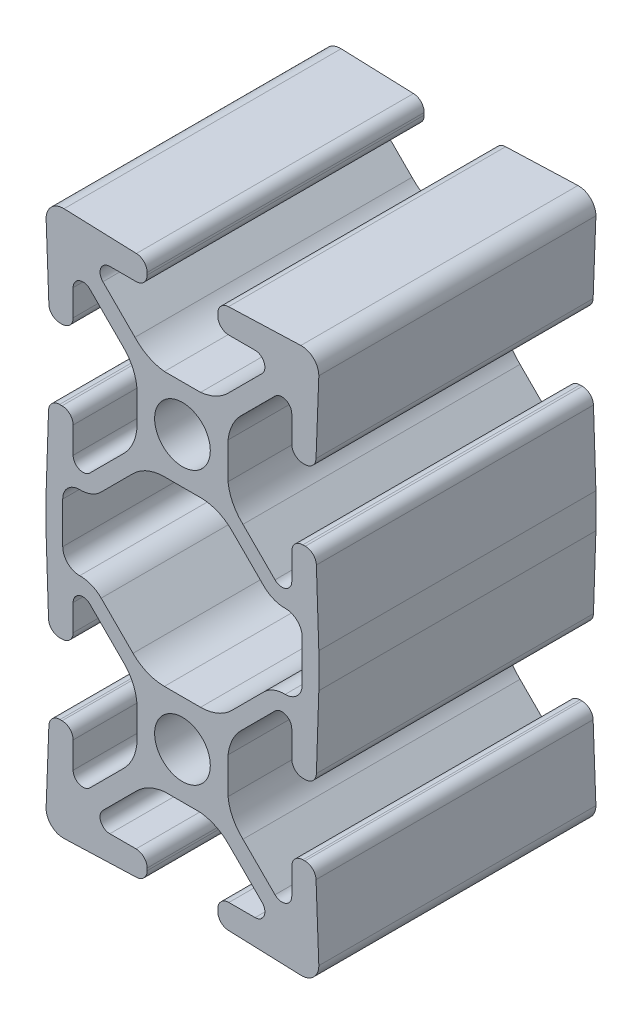
SolidWorks part; units mm, degrees
material "6061 Alloy"
ref_plane "Front" through (0, 0, 0) normal (0, 0, 1) x (1, 0, 0)
ref_plane "Top" through (0, 0, 0) normal (0, 1, 0) x (1, 0, 0)
ref_plane "Right" through (0, 0, 0) normal (1, 0, 0) x (0, 0, -1)
sketch "Sketch1" plane through (0, 0, 0) normal (0, 0, 1) x (1, 0, 0)
  line L0 (-4.5322, 5.3683) -> (-7.4494, 8.2856)
  line L1 (-10.976, 10.6094) -> (-10.976, 14.3906)
  line L2 (1.6585, 4.178) -> (-1.6585, 4.178)
  line L3 (7.4494, 8.2856) -> (4.5322, 5.3683)
  line L4 (-7.4494, 16.7144) -> (-4.5322, 19.6317)
  line L5 (-1.6585, 20.822) -> (1.6585, 20.822)
  line L6 (10.976, 14.3906) -> (10.976, 10.6094)
  line L7 (4.5322, 19.6317) -> (7.4494, 16.7144)
  line L8 (-8.4836, 7.2939) -> (-5.5451, 4.3554)
  line L9 (-10.02, 4.2545) -> (-10.02, 6.6575)
  line L10 (-4.178, 1.6585) -> (-4.178, -1.6585)
  line L11 (-11.2584, 3.2377) -> (-11.036, 3.2385)
  line L12 (-5.5451, -4.3554) -> (-8.4836, -7.2939)
  line L13 (-12.5, 10.9125) -> (-12.2773, 4.22)
  line L14 (-12.5, 14.0875) -> (-12.5, 10.9125)
  line L15 (-10.02, -6.6575) -> (-10.02, -4.2545)
  line L16 (-12.2773, 20.78) -> (-12.5, 14.0875)
  line L17 (-11.036, -3.2385) -> (-11.2263, -3.2379)
  line L18 (-11.036, 21.7615) -> (-11.2584, 21.7623)
  line L19 (-12.2451, -4.2152) -> (-12.5, -10.9135)
  line L20 (-10.02, 18.3425) -> (-10.02, 20.7455)
  line L21 (-10.8555, -12.5) -> (-4.2218, -12.2615)
  line L22 (-5.5451, 20.6446) -> (-8.4836, 17.7061)
  line L23 (-3.2385, -11.246) -> (-3.2385, -11.036)
  line L24 (-4.178, 26.6585) -> (-4.178, 23.3415)
  line L25 (-4.2545, -10.02) -> (-6.6575, -10.02)
  line L26 (-8.4836, 32.2939) -> (-5.5451, 29.3554)
  line L27 (-7.2939, -8.4836) -> (-4.3554, -5.5451)
  line L28 (-10.02, 29.2545) -> (-10.02, 31.6575)
  line L29 (-1.6585, -4.178) -> (1.6585, -4.178)
  line L30 (-11.2263, 28.2379) -> (-11.036, 28.2385)
  line L31 (4.3554, -5.5451) -> (7.2939, -8.4836)
  line L32 (-12.5, 35.9135) -> (-12.2451, 29.2152)
  line L33 (6.6575, -10.02) -> (4.2545, -10.02)
  line L34 (-4.2218, 37.2615) -> (-10.8555, 37.5)
  line L35 (3.2385, -11.036) -> (3.2385, -11.246)
  line L36 (-3.2385, 36.036) -> (-3.2385, 36.246)
  line L37 (4.2218, -12.2615) -> (10.8555, -12.5)
  line L38 (-6.6575, 35.02) -> (-4.2545, 35.02)
  line L39 (12.5, -10.9135) -> (12.2451, -4.2152)
  line L40 (-4.3554, 30.5451) -> (-7.2939, 33.4836)
  line L41 (11.2263, -3.2379) -> (11.036, -3.2385)
  line L42 (1.6585, 29.178) -> (-1.6585, 29.178)
  line L43 (10.02, -4.2545) -> (10.02, -6.6575)
  line L44 (7.2939, 33.4836) -> (4.3554, 30.5451)
  line L45 (8.4836, -7.2939) -> (5.5451, -4.3554)
  line L46 (4.2545, 35.02) -> (6.6575, 35.02)
  line L47 (4.178, -1.6585) -> (4.178, 1.6585)
  line L48 (3.2385, 36.246) -> (3.2385, 36.036)
  line L49 (5.5451, 4.3554) -> (8.4836, 7.2939)
  line L50 (10.8555, 37.5) -> (4.2218, 37.2615)
  line L51 (10.02, 6.6575) -> (10.02, 4.2545)
  line L52 (12.2451, 29.2152) -> (12.5, 35.9135)
  line L53 (11.036, 3.2385) -> (11.2584, 3.2377)
  line L54 (11.036, 28.2385) -> (11.2263, 28.2379)
  line L55 (12.2773, 4.22) -> (12.5, 10.9125)
  line L56 (10.02, 31.6575) -> (10.02, 29.2545)
  line L57 (12.5, 10.9125) -> (12.5, 14.0875)
  line L58 (12.5, 14.0875) -> (12.2773, 20.78)
  line L59 (5.5451, 29.3554) -> (8.4836, 32.2939)
  line L60 (11.2584, 21.7623) -> (11.036, 21.7615)
  line L61 (4.178, 23.3415) -> (4.178, 26.6585)
  line L62 (10.02, 20.7455) -> (10.02, 18.3425)
  line L63 (8.4836, 17.7061) -> (5.5451, 20.6446)
  arc A0 (-7.4494, 8.2856) -> (-9.4184, 9.0858) centre (-9.3594, 6.4083) ccw
  arc A1 (-10.976, 10.6094) -> (-9.4184, 9.0858) centre (-9.452, 10.6094) ccw
  arc A2 (-4.5322, 5.3683) -> (-1.6585, 4.178) centre (-1.6585, 8.242) ccw
  arc A3 (-9.4184, 15.9142) -> (-10.976, 14.3906) centre (-9.452, 14.3906) ccw
  arc A4 (1.6585, 4.178) -> (4.5322, 5.3683) centre (1.6585, 8.242) ccw
  arc A5 (-9.4184, 15.9142) -> (-7.4494, 16.7144) centre (-9.3594, 18.5917) ccw
  arc A6 (9.4184, 9.0858) -> (7.4494, 8.2856) centre (9.3594, 6.4083) ccw
  arc A7 (-1.6585, 20.822) -> (-4.5322, 19.6317) centre (-1.6585, 16.758) ccw
  arc A8 (9.4184, 9.0858) -> (10.976, 10.6094) centre (9.452, 10.6094) ccw
  arc A9 (4.5322, 19.6317) -> (1.6585, 20.822) centre (1.6585, 16.758) ccw
  arc A10 (10.976, 14.3906) -> (9.4184, 15.9142) centre (9.452, 14.3906) ccw
  arc A11 (7.4494, 16.7144) -> (9.4184, 15.9142) centre (9.3594, 18.5917) ccw
  arc A12 (-8.4836, 7.2939) -> (-10.02, 6.6575) centre (-9.12, 6.6575) ccw
  arc A13 (-4.178, 1.6585) -> (-5.5451, 4.3554) centre (-8.422, 1.2021) ccw
  arc A14 (-11.036, 3.2385) -> (-10.02, 4.2545) centre (-11.036, 4.2545) ccw
  arc A15 (-5.5451, -4.3554) -> (-4.178, -1.6585) centre (-8.422, -1.2021) ccw
  arc A16 (-12.2773, 4.22) -> (-11.2584, 3.2377) centre (-11.2618, 4.2537) ccw
  arc A17 (-10.02, -6.6575) -> (-8.4836, -7.2939) centre (-9.12, -6.6575) ccw
  arc A18 (-10.02, -4.2545) -> (-11.036, -3.2385) centre (-11.036, -4.2545) ccw
  arc A19 (-11.2584, 21.7623) -> (-12.2773, 20.78) centre (-11.2618, 20.7463) ccw
  arc A20 (-11.2263, -3.2379) -> (-12.2451, -4.2152) centre (-11.2298, -4.2539) ccw
  arc A21 (-10.02, 20.7455) -> (-11.036, 21.7615) centre (-11.036, 20.7455) ccw
  arc A22 (-12.5, -10.9135) -> (-10.8555, -12.5) centre (-10.9125, -10.9135) ccw
  arc A23 (-10.02, 18.3425) -> (-8.4836, 17.7061) centre (-9.12, 18.3425) ccw
  arc A24 (-4.2218, -12.2615) -> (-3.2385, -11.246) centre (-4.2545, -11.246) ccw
  arc A25 (-5.5451, 20.6446) -> (-4.178, 23.3415) centre (-8.422, 23.7979) ccw
  arc A26 (-3.2385, -11.036) -> (-4.2545, -10.02) centre (-4.2545, -11.036) ccw
  arc A27 (-4.178, 26.6585) -> (-5.5451, 29.3554) centre (-8.422, 26.2021) ccw
  arc A28 (-7.2939, -8.4836) -> (-6.6575, -10.02) centre (-6.6575, -9.12) ccw
  arc A29 (-8.4836, 32.2939) -> (-10.02, 31.6575) centre (-9.12, 31.6575) ccw
  arc A30 (-1.6585, -4.178) -> (-4.3554, -5.5451) centre (-1.2021, -8.422) ccw
  arc A31 (-11.036, 28.2385) -> (-10.02, 29.2545) centre (-11.036, 29.2545) ccw
  arc A32 (4.3554, -5.5451) -> (1.6585, -4.178) centre (1.2021, -8.422) ccw
  arc A33 (-12.2451, 29.2152) -> (-11.2263, 28.2379) centre (-11.2298, 29.2539) ccw
  arc A34 (6.6575, -10.02) -> (7.2939, -8.4836) centre (6.6575, -9.12) ccw
  arc A35 (-10.8555, 37.5) -> (-12.5, 35.9135) centre (-10.9125, 35.9135) ccw
  arc A36 (4.2545, -10.02) -> (3.2385, -11.036) centre (4.2545, -11.036) ccw
  arc A37 (-3.2385, 36.246) -> (-4.2218, 37.2615) centre (-4.2545, 36.246) ccw
  arc A38 (3.2385, -11.246) -> (4.2218, -12.2615) centre (4.2545, -11.246) ccw
  arc A39 (-4.2545, 35.02) -> (-3.2385, 36.036) centre (-4.2545, 36.036) ccw
  arc A40 (10.8555, -12.5) -> (12.5, -10.9135) centre (10.9125, -10.9135) ccw
  arc A41 (-6.6575, 35.02) -> (-7.2939, 33.4836) centre (-6.6575, 34.12) ccw
  arc A42 (12.2451, -4.2152) -> (11.2263, -3.2379) centre (11.2298, -4.2539) ccw
  arc A43 (-4.3554, 30.5451) -> (-1.6585, 29.178) centre (-1.2021, 33.422) ccw
  arc A44 (11.036, -3.2385) -> (10.02, -4.2545) centre (11.036, -4.2545) ccw
  arc A45 (1.6585, 29.178) -> (4.3554, 30.5451) centre (1.2021, 33.422) ccw
  arc A46 (8.4836, -7.2939) -> (10.02, -6.6575) centre (9.12, -6.6575) ccw
  arc A47 (7.2939, 33.4836) -> (6.6575, 35.02) centre (6.6575, 34.12) ccw
  arc A48 (4.178, -1.6585) -> (5.5451, -4.3554) centre (8.422, -1.2021) ccw
  arc A49 (3.2385, 36.036) -> (4.2545, 35.02) centre (4.2545, 36.036) ccw
  arc A50 (5.5451, 4.3554) -> (4.178, 1.6585) centre (8.422, 1.2021) ccw
  arc A51 (4.2218, 37.2615) -> (3.2385, 36.246) centre (4.2545, 36.246) ccw
  arc A52 (10.02, 6.6575) -> (8.4836, 7.2939) centre (9.12, 6.6575) ccw
  arc A53 (12.5, 35.9135) -> (10.8555, 37.5) centre (10.9125, 35.9135) ccw
  arc A54 (10.02, 4.2545) -> (11.036, 3.2385) centre (11.036, 4.2545) ccw
  arc A55 (11.2263, 28.2379) -> (12.2451, 29.2152) centre (11.2298, 29.2539) ccw
  arc A56 (11.2584, 3.2377) -> (12.2773, 4.22) centre (11.2618, 4.2537) ccw
  arc A57 (10.02, 29.2545) -> (11.036, 28.2385) centre (11.036, 29.2545) ccw
  arc A58 (10.02, 31.6575) -> (8.4836, 32.2939) centre (9.12, 31.6575) ccw
  arc A59 (12.2773, 20.78) -> (11.2584, 21.7623) centre (11.2618, 20.7463) ccw
  arc A60 (5.5451, 29.3554) -> (4.178, 26.6585) centre (8.422, 26.2021) ccw
  arc A61 (11.036, 21.7615) -> (10.02, 20.7455) centre (11.036, 20.7455) ccw
  arc A62 (4.178, 23.3415) -> (5.5451, 20.6446) centre (8.422, 23.7979) ccw
  arc A63 (8.4836, 17.7061) -> (10.02, 18.3425) centre (9.12, 18.3425) ccw
  circle A64 centre (0, 0) radius 2.5527
  circle A65 centre (0, 25) radius 2.5527
extrude "Extrude1" add sketch "Sketch1" along normal blind 25.4
